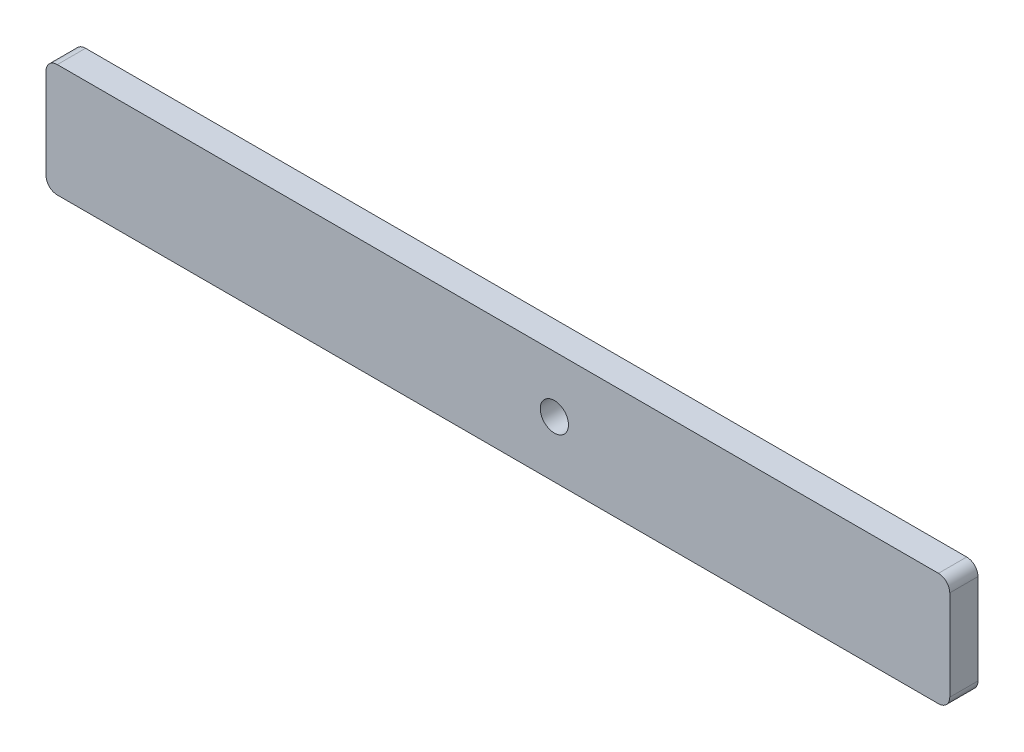
SolidWorks part; units mm, degrees
ref_plane "Front Plane" through (0, 0, 0) normal (0, 0, 1) x (1, 0, 0)
ref_plane "Top Plane" through (0, 0, 0) normal (0, 1, 0) x (1, 0, 0)
ref_plane "Right Plane" through (0, 0, 0) normal (1, 0, 0) x (0, 0, -1)
sketch "Sketch1" plane through (0, 0, 0) normal (0, 0, 1) x (1, 0, 0)
  line L1 (-99.06, 12.7) -> (99.06, 12.7)
  line L2 (-101.6, 10.16) -> (-101.6, -10.16)
  line L3 (-99.06, -12.7) -> (99.06, -12.7)
  line L4 (101.6, 10.16) -> (101.6, -10.16)
  line L5 (-101.6, 12.7) -> (101.6, -12.7) construction
  line L6 (-101.6, -12.7) -> (101.6, 12.7) construction
  arc A0 (99.06, -12.7) -> (101.6, -10.16) centre (99.06, -10.16) ccw
  arc A1 (99.06, 12.7) -> (101.6, 10.16) centre (99.06, 10.16) cw
  arc A2 (-101.6, -10.16) -> (-99.06, -12.7) centre (-99.06, -10.16) ccw
  arc A3 (-99.06, 12.7) -> (-101.6, 10.16) centre (-99.06, 10.16) ccw
  circle A4 centre (12.7, 0) radius 3.175
  point P0 (0, 0)
  dimension "D3" = 2.54
  dimension "D4" = 6.35
  dimension "D1" = 25.4
  dimension "D2" = 203.2
  dimension "D5" = 88.9
extrude "Boss-Extrude1" add sketch "Sketch1" along normal blind 6.35
